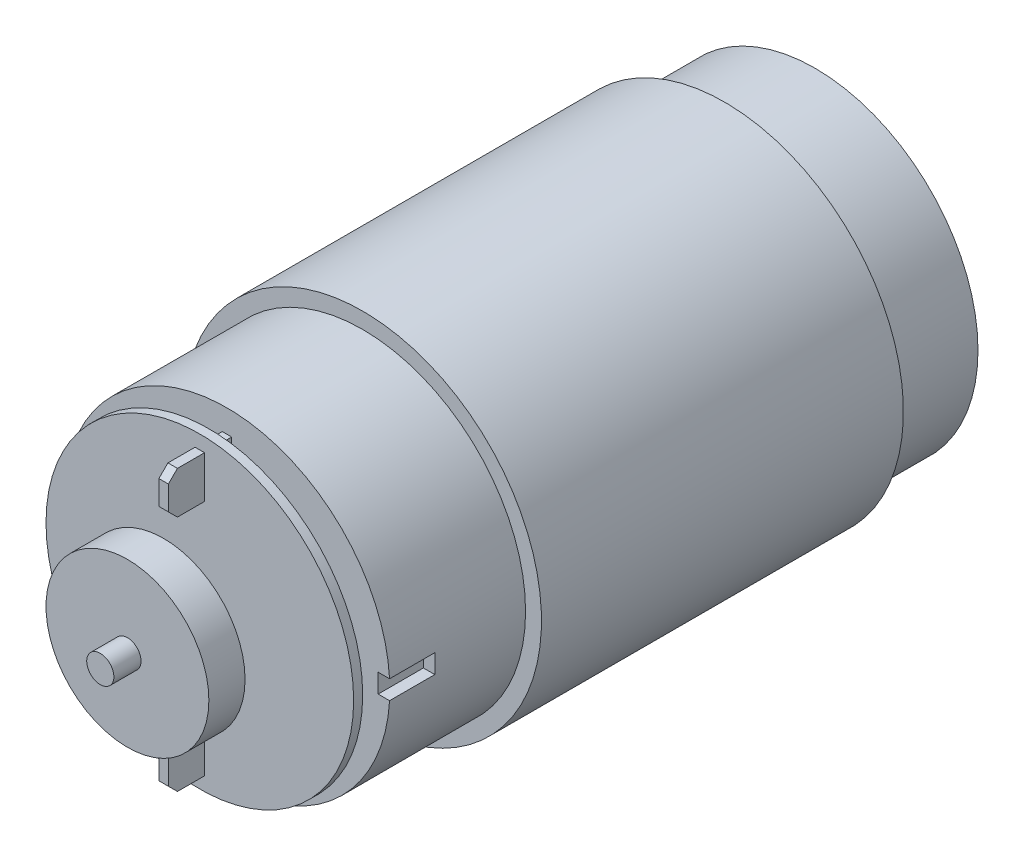
SolidWorks part; units mm, degrees
ref_plane "Front Plane" through (0, 0, 0) normal (0, 0, 1) x (1, 0, 0)
ref_plane "Top Plane" through (0, 0, 0) normal (0, 1, 0) x (1, 0, 0)
ref_plane "Right Plane" through (0, 0, 0) normal (1, 0, 0) x (0, 0, -1)
sketch "Sketch1" plane through (0, 0, 0) normal (0, 0, 1) x (1, 0, 0)
  circle A0 centre (0, 0) radius 18
  dimension "D1" = 36
extrude "Boss-Extrude1" add sketch "Sketch1" along normal blind 65
sketch "Sketch2" plane through (0, 0, 0) normal (0, 0, -1) x (-1, 0, 0)
  circle A0 centre (0, 0) radius 18
  circle A1 centre (0, 0) radius 19.7581
extrude "Boss-Extrude2" add sketch "Sketch2" against normal blind 40 from offset 10 offset against normal yes
sketch "Sketch3" plane through (0, 0, 65) normal (0, 0, 1) x (1, 0, 0)
  circle A0 centre (0, 0) radius 1.5
  dimension "D1" = 3
extrude "Boss-Extrude3" add sketch "Sketch3" along normal blind 14
sketch "Sketch4" plane through (0, 0, 65) normal (0, 0, 1) x (1, 0, 0)
  circle A0 centre (0, 0) radius 9
  dimension "D1" = 18
extrude "Boss-Extrude4" add sketch "Sketch4" along normal blind 2
sketch "Sketch5" plane through (0, 0, 67) normal (0, 0, 1) x (1, 0, 0)
  circle A0 centre (0, 0) radius 17
  dimension "D1" = 34
extrude "Boss-Extrude5" add sketch "Sketch5" along normal blind 1
sketch "Sketch6" plane through (0, 0, 79) normal (0, 0, 1) x (1, 0, 0)
  circle A0 centre (0, 0) radius 9
  dimension "D1" = 18
extrude "Boss-Extrude6" add sketch "Sketch6" against normal blind 4 from offset 3 offset against normal yes
sketch "Sketch7" plane through (0, 0, 65) normal (0, 0, 1) x (1, 0, 0)
  line L0 (16.7093, 1.0484) -> (16.7093, -1.0484)
  line L1 (-21.1771, -1.0484) -> (-16.6074, -1.0484)
  line L2 (-21.1771, -1.0484) -> (-21.1771, 1.0484)
  line L3 (-21.1771, 1.0484) -> (-16.6074, 1.0484)
  line L4 (21.1771, -1.0484) -> (21.1771, 1.0484)
  line L5 (-21.1771, -1.0484) -> (-16.6074, -0.8221) construction
  line L6 (-21.1771, 1.0484) -> (-16.6074, 0.8221) construction
  line L7 (-16.6074, 1.0484) -> (-16.6074, -1.0484)
  line L8 (16.7093, 1.0484) -> (21.1771, 1.0484)
  line L9 (16.7093, -0.8272) -> (21.1771, -1.0484) construction
  line L10 (16.7093, 0.8272) -> (21.1771, 1.0484) construction
  line L11 (16.7093, -1.0484) -> (21.1771, -1.0484)
  point P0 (0, 0)
extrude "Cut-Extrude1" cut sketch "Sketch7" against normal blind 5
sketch "Sketch8" plane through (0, 0, 65) normal (0, 0, 1) x (1, 0, 0)
  line L0 (-0.5242, 10.7982) -> (0.5242, 10.7982)
  line L1 (-0.5242, -15.4635) -> (0.5242, -15.4635)
  line L2 (-0.5242, -15.4635) -> (-0.5242, -10.7982)
  line L3 (-0.5242, 15.4635) -> (0.5242, 15.4635)
  line L4 (0.5242, -15.4635) -> (0.5242, -10.7982)
  line L5 (-0.5242, -15.4635) -> (-0.366, -10.7982) construction
  line L6 (-0.5242, 15.4635) -> (-0.366, 10.7982) construction
  line L7 (-0.5242, -10.7982) -> (0.5242, -10.7982)
  line L10 (0.5242, 10.7982) -> (0.5242, 15.4635)
  line L11 (0.366, -10.7982) -> (0.5242, -15.4635) construction
  line L12 (0.366, 10.7982) -> (0.5242, 15.4635) construction
  line L13 (-0.5242, 10.7982) -> (-0.5242, 15.4635)
  point P0 (0, 0)
extrude "Boss-Extrude7" add sketch "Sketch8" along normal blind 7
chamfer "Chamfer1" distance 1 angle 45 4 edges at (0, 15.4635, 72) (0, 10.7982, 72) (0, -10.7982, 72) (0, -15.4635, 72)
